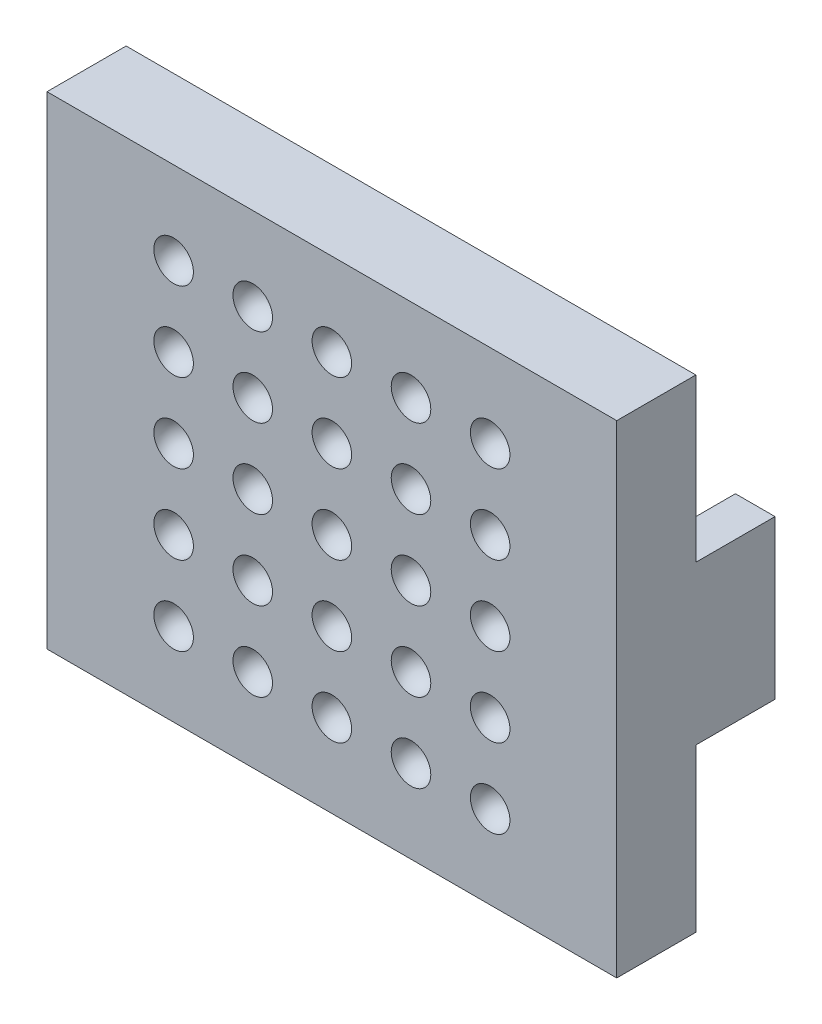
SolidWorks part; units mm, degrees
ref_plane "Front" through (0, 0, 0) normal (0, 0, 1) x (1, 0, 0)
ref_plane "Top" through (0, 0, 0) normal (0, 1, 0) x (1, 0, 0)
ref_plane "Right" through (0, 0, 0) normal (1, 0, 0) x (0, 0, -1)
sketch "Sketch1" plane through (0, 0, 0) normal (0, 0, 1) x (1, 0, 0)
  line L1 (-36, -30.5) -> (36, -30.5)
  line L2 (-36, -30.5) -> (-36, 30.5)
  line L3 (-36, 30.5) -> (36, 30.5)
  line L4 (36, -30.5) -> (36, 30.5)
  line L5 (0, 30.5) -> (0, -30.5) construction
  line L6 (-36, 0) -> (36, 0) construction
  point P0 (0, 0)
  dimension "D1" = 72
  dimension "D2" = 61
extrude "Mold Top" add sketch "Sketch1" along normal blind 10
sketch "Sketch3" plane through (0, 0, 0) normal (0, 0, -1) x (-1, 0, 0)
  line L0 (-36, 0) -> (36, 0) construction
  line L1 (36, 30.5) -> (36, -30.5) construction
  line L2 (-36, -30.5) -> (-36, 30.5) construction
  line L3 (-36, 10) -> (-31, 10)
  line L4 (-36, 10) -> (-36, -10)
  line L5 (-36, -10) -> (-31, -10)
  line L6 (-31, 10) -> (-31, -10)
  line L7 (-33.5, -10) -> (-33.5, 10) construction
  line L8 (-36, 0) -> (-31, 0) construction
  point P6 (0, 0)
  point P507 (-33.5, 0)
  dimension "D1" = 5
  dimension "D2" = 20
extrude "Handle 1" add sketch "Sketch3" along normal blind 10
mirror "Handle 2" about plane through (0, 0, 0) normal (1, 0, 0) of "Handle 1"
sketch "Sketch5" plane through (0, 0, 10) normal (0, 0, 1) x (1, 0, 0)
  line L0 (0, 2.5) -> (0, -2.5) construction
  line L1 (0, 2.5) -> (0, -2.5)
  arc A0 (0, -2.5) -> (0, 2.5) centre (0, 0) ccw
  dimension "D1" = 5
revolve "Cut-Revolve1" cut sketch "Sketch5" angle 360 about L0
pattern_linear "LPattern1" count 3 spacing 10 along (0, -1, 0) count 3 spacing 10 along (-1, 0, 0) of "Cut-Revolve1"
pattern_linear "LPattern2" count 3 spacing 10 along (1, 0, 0) count 3 spacing 10 along (0, 1, 0) of "LPattern1", "Cut-Revolve1"
sketch "Sketch6" plane through (0, 0, 10) normal (0, 0, 1) x (1, 0, 0)
  circle A0 centre (0, 0) radius 0.5
  dimension "D1" = 1
extrude "Cut-Extrude1" cut sketch "Sketch6" against normal through all
pattern_linear "LPattern3" count 3 spacing 10 along (0, -1, 0) count 3 spacing 10 along (-1, 0, 0) of "Cut-Extrude1"
pattern_linear "LPattern4" count 3 spacing 10 along (1, 0, 0) count 3 spacing 10 along (0, 1, 0) of "LPattern3", "Cut-Extrude1"
